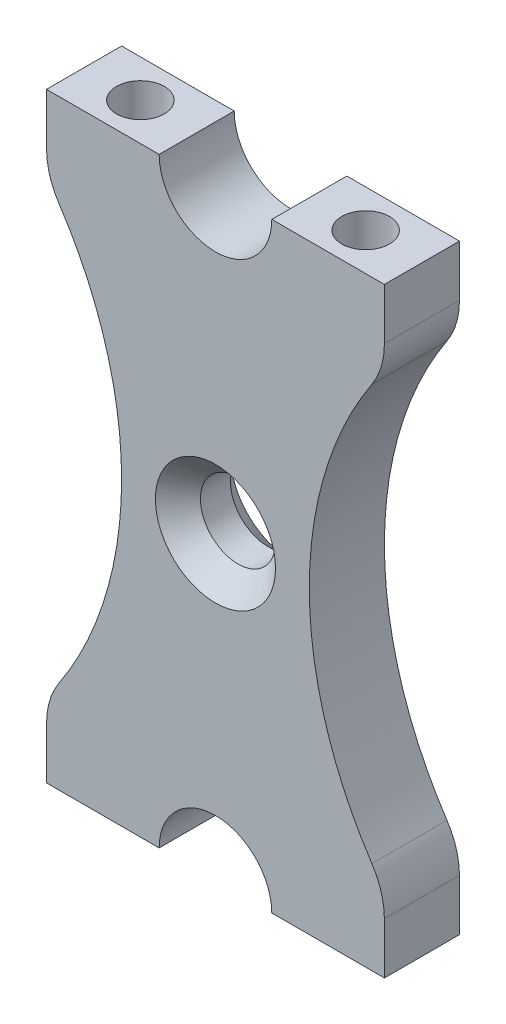
SolidWorks part; units mm, degrees
material "5052-H32"
ref_plane "Front Plane" through (0, 0, 0) normal (0, 0, 1) x (1, 0, 0)
ref_plane "Top Plane" through (0, 0, 0) normal (0, 1, 0) x (1, 0, 0)
ref_plane "Right Plane" through (0, 0, 0) normal (1, 0, 0) x (0, 0, -1)
sketch "Sketch1" plane through (0, 0, 0) normal (0, 0, 1) x (1, 0, 0)
  line L1 (-14.2875, 25.4) -> (14.2875, 25.4)
  line L2 (-14.2875, 25.4) -> (-14.2875, -25.4)
  line L3 (-14.2875, -25.4) -> (14.2875, -25.4)
  line L4 (14.2875, 25.4) -> (14.2875, -25.4)
  line L5 (-14.2875, 25.4) -> (14.2875, -25.4) construction
  line L6 (-14.2875, -25.4) -> (14.2875, 25.4) construction
  point P0 (0, 0)
  dimension "D1" = 50.8
  dimension "D2" = 28.575
extrude "Boss-Extrude1" add sketch "Sketch1" along normal blind 6.35
hole_wizard "#10-32 Tapped Hole1" positions "Sketch2" profile "Sketch3" tap size "#10-32" standard "ANSI Inch"
sketch "Sketch2" plane through (0, 25.4, 0) normal (0, 1, 0) x (1, 0, 0)
  line L0 (-14.2875, -3.175) -> (14.2875, -3.175)
  line L1 (-14.2875, -6.35) -> (-14.2875, 0) construction
  line L2 (14.2875, -6.35) -> (14.2875, 0) construction
  point P0 (-9.525, -3.175)
  point P4 (9.525, -3.175)
  dimension "D1" = 4.7625
  dimension "D2" = 4.7625
sketch "Sketch3" plane through (-9.525, 25.4, 3.175) normal (1, 0, 0) x (0, 0, 1)
  line L0 (0, 0) -> (0, 10.8653)
  line L1 (0, 10.8653) -> (2.0193, 9.652)
  line L2 (2.0193, 9.652) -> (2.0193, 0)
  line L5 (2.0193, 0) -> (0, 0)
  line L10 (0, 10.8653) -> (-2.0193, 9.652) construction
  line L11 (0, -6.35) -> (0, 107.95) construction
  dimension "Tap Drill Dia." = 4.0386
  dimension "Tap Drill Depth" = 9.652
  dimension "Drill Angle" = 118
cosmetic thread "Hole Thread1" parameters "D1"=6.35, "D2"=4.826
cosmetic thread "Hole Thread2" parameters "D1"=6.35, "D2"=4.826
mirror "Mirror1" about plane through (0, 0, 0) normal (0, 1, 0) of "#10-32 Tapped Hole1"
hole_wizard "1/4 (0.25) Diameter Hole1" positions "Sketch4" profile "Sketch5" hole size "1/4" standard "ANSI Inch"
sketch "Sketch4" plane through (0, 0, 6.35) normal (0, 0, 1) x (1, 0, 0)
  point P0 (0, 0)
sketch "Sketch5" plane through (0, 0, 6.35) normal (1, 0, 0) x (0, -1, 0)
  line L0 (0, 0) -> (0, 12.5757)
  line L1 (0, 12.5757) -> (3.175, 10.668)
  line L2 (3.175, 10.668) -> (3.175, 0)
  line L5 (3.175, 0) -> (0, 0)
  line L10 (0, 12.5757) -> (-3.175, 10.668) construction
  line L11 (0, -6.35) -> (0, 107.95) construction
  dimension "Hole Dia." = 6.35
  dimension "Hole Depth" = 10.668
  dimension "Drill Angle" = 118
chamfer "Chamfer1" distance 1.905 angle 45 2 edges at (3.175, 0, 0) (3.175, 0, 6.35)
sketch "Sketch6" plane through (0, 0, 6.35) normal (0, 0, 1) x (1, 0, 0)
  line L0 (-14.2875, 25.4) -> (-14.2875, -25.4) construction
  line L1 (14.2875, -25.4) -> (14.2875, 25.4) construction
  line L2 (-39.6875, 0) -> (39.6875, 0) construction
  line L3 (14.2875, 25.4) -> (-14.2875, 25.4) construction
  line L4 (-14.2875, 19.05) -> (-14.2875, -19.05)
  line L5 (14.2875, -19.05) -> (14.2875, 19.05)
  line L6 (-14.2875, -25.4) -> (14.2875, -25.4) construction
  line L7 (-4.7625, 25.4) -> (4.7625, 25.4)
  line L8 (-4.7625, -25.4) -> (4.7625, -25.4)
  arc A0 (-14.2875, 19.05) -> (-14.2875, -19.05) centre (-39.6875, 0) cw
  arc A1 (14.2875, 19.05) -> (14.2875, -19.05) centre (39.6875, 0) ccw
  arc A3 (-4.7625, 25.4) -> (4.7625, 25.4) centre (0, 25.4) ccw
  arc A4 (-4.7625, -25.4) -> (4.7625, -25.4) centre (0, -25.4) cw
  point P8 (0, 0)
  dimension "D1" = 6.35
  dimension "D2" = 31.75
  dimension "D3" = 4.7625
extrude "Cut-Extrude1" cut sketch "Sketch6" against normal through all
fillet "Fillet1" radius 6.35 4 edges at (14.2875, -19.05, 3.175) (14.2875, 19.05, 3.175) (-14.2875, 19.05, 3.175) (-14.2875, -19.05, 3.175)
